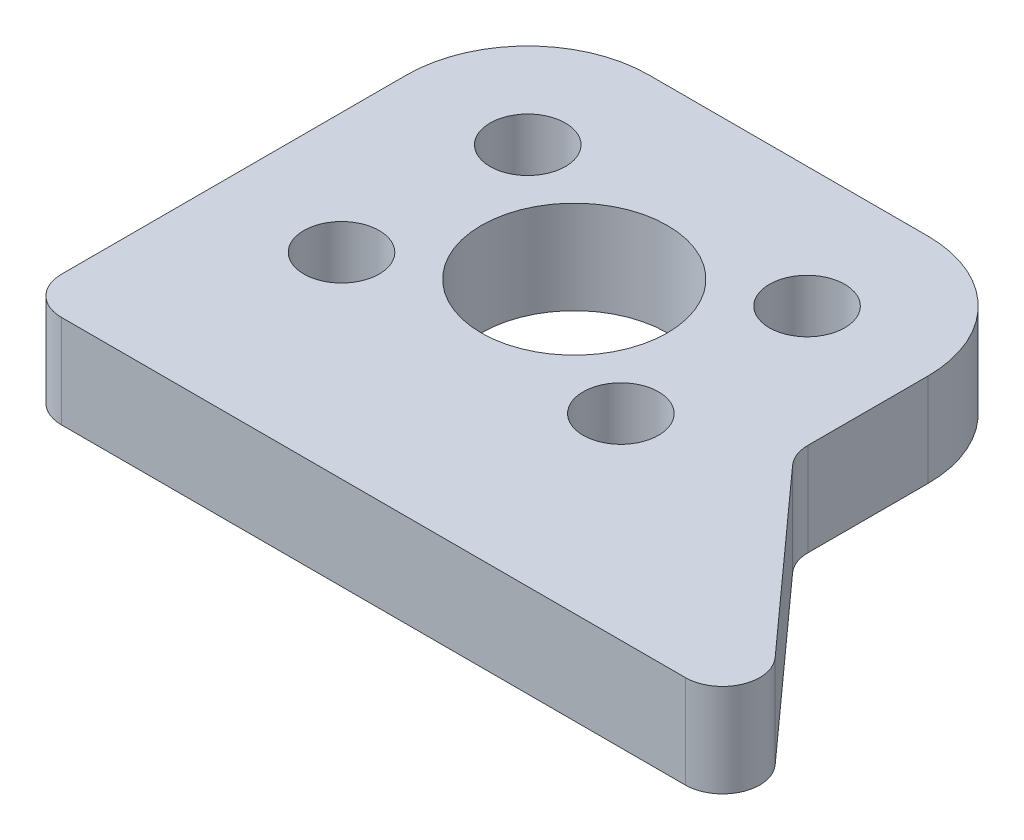
SolidWorks part; units mm, degrees
material "Thornel Mat VMA"
ref_plane "前视基准面" through (0, 0, 0) normal (0, 0, 1) x (1, 0, 0)
ref_plane "上视基准面" through (0, 0, 0) normal (0, 1, 0) x (1, 0, 0)
ref_plane "右视基准面" through (0, 0, 0) normal (1, 0, 0) x (0, 0, -1)
other "Configuration Table"
sketch "草图1" plane through (0, 0, 0) normal (0, 1, 0) x (1, 0, 0)
  line L0 (-7.5, 11.5) -> (7.5, 11.5)
  line L1 (-7.5, -5) -> (7.5, -5) construction
  line L2 (-7.5, -5) -> (-7.5, 5) construction
  line L3 (-7.5, 5) -> (7.5, 5) construction
  line L4 (7.5, -5) -> (7.5, 5) construction
  line L5 (-7.5, -5) -> (7.5, 5) construction
  line L6 (-7.5, 5) -> (7.5, -5) construction
  line L7 (7.5, 5) -> (26, -15.5463)
  line L8 (-14, 5) -> (-14, -15.5463)
  line L9 (-14, -15.5463) -> (26, -15.5463)
  line L10 (14, 5) -> (14, -2.219)
  circle A0 centre (-7.5, 5) radius 6.5
  circle A1 centre (7.5, 5) radius 6.5
  circle A2 centre (-7.5, 5) radius 2.025
  circle A3 centre (7.5, 5) radius 2.025
  circle A4 centre (-7.5, -5) radius 2.025
  circle A5 centre (7.5, -5) radius 2.025
  point P0 (0, 0)
  dimension "D3" = 13
  dimension "D4" = 4.05
  dimension "D1" = 15
  dimension "D2" = 10
  dimension "D5" = 42
  dimension "D6" = 40
extrude "凸台-拉伸1" add sketch "草图1" along normal blind 5
fillet "圆角1" radius 2 3 edges at (14, 2.5, 2.219) (-14, 2.5, 15.5463) (26, 2.5, 15.5463)
sketch "草图2" plane through (0, 5, 0) normal (0, 1, 0) x (1, 0, 0)
  circle A0 centre (0, 0) radius 5
  dimension "D1" = 10
extrude "切除-拉伸1" cut sketch "草图2" against normal blind 5
